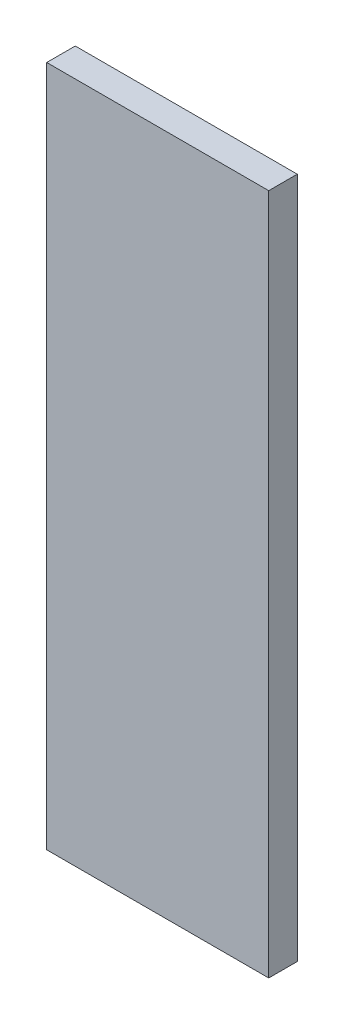
SolidWorks part; units mm, degrees
material "Balsa"
ref_plane "Front Plane" through (0, 0, 0) normal (0, 0, 1) x (1, 0, 0)
ref_plane "Top Plane" through (0, 0, 0) normal (0, 1, 0) x (1, 0, 0)
ref_plane "Right Plane" through (0, 0, 0) normal (1, 0, 0) x (0, 0, -1)
sketch "Sketch1" plane through (0, 0, 0) normal (0, 0, 1) x (1, 0, 0)
  line L1 (-70, 215) -> (70, 215)
  line L2 (-70, 215) -> (-70, -215)
  line L3 (-70, -215) -> (70, -215)
  line L4 (70, 215) -> (70, -215)
  line L5 (-70, 215) -> (70, -215) construction
  line L6 (-70, -215) -> (70, 215) construction
  point P0 (0, 0)
  dimension "D1" = 140
  dimension "D2" = 430
extrude "Boss-Extrude1" add sketch "Sketch1" along normal blind 18
